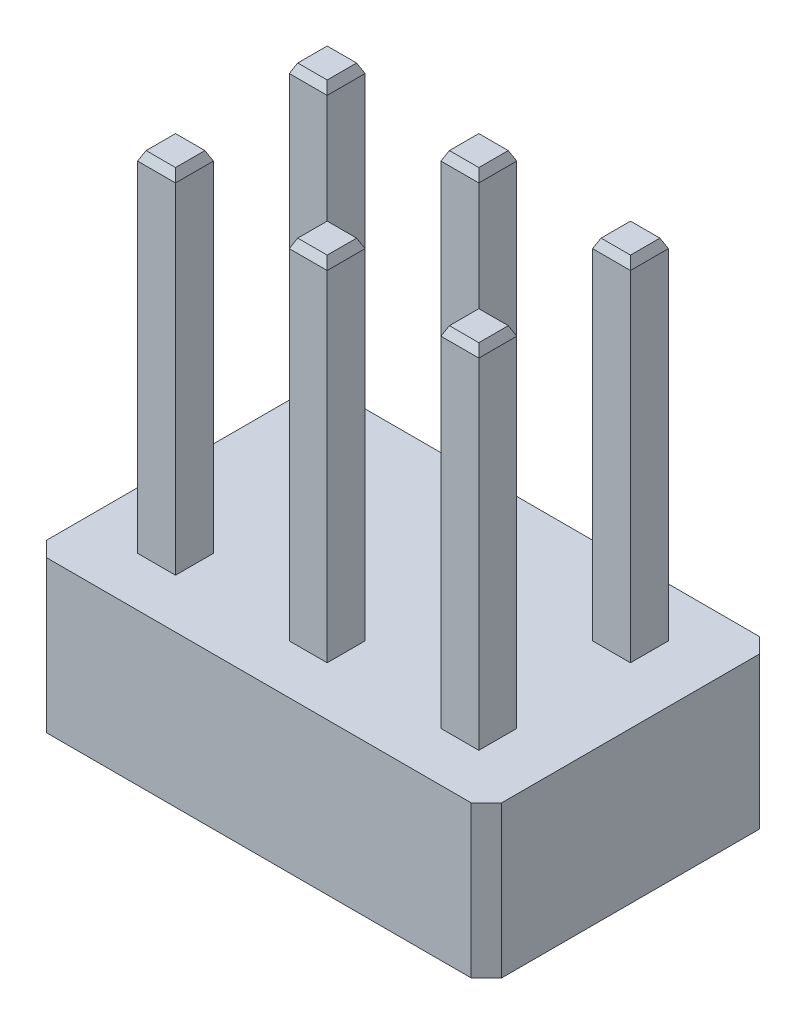
SolidWorks part; units mm, degrees
material "ABS PC"
ref_plane "Front Plane" through (0, 0, 0) normal (0, 0, 1) x (1, 0, 0)
ref_plane "Top Plane" through (0, 0, 0) normal (0, 1, 0) x (1, 0, 0)
ref_plane "Right Plane" through (0, 0, 0) normal (1, 0, 0) x (0, 0, -1)
sketch "Sketch1" plane through (0, 0, 0) normal (0, 1, 0) x (1, 0, 0)
  line L1 (0, 0) -> (7.62, 0)
  line L2 (0, 0) -> (0, 4.826)
  line L3 (0, 4.826) -> (7.62, 4.826)
  line L4 (7.62, 0) -> (7.62, 4.826)
  dimension "D1" = 7.62
  dimension "D2" = 4.826
extrude "Boss-Extrude1" add sketch "Sketch1" along normal blind 2.54
sketch "Sketch2" plane through (0, 2.54, 0) normal (0, 1, 0) x (1, 0, 0)
  line L0 (0, 0) -> (7.62, 0) construction
  line L1 (0.9525, 0.8255) -> (1.5875, 0.8255)
  line L2 (0.9525, 0.8255) -> (0.9525, 1.4605)
  line L3 (0.9525, 1.4605) -> (1.5875, 1.4605)
  line L4 (1.5875, 0.8255) -> (1.5875, 1.4605)
  line L5 (0.9525, 0.8255) -> (1.5875, 1.4605) construction
  line L6 (0.9525, 1.4605) -> (1.5875, 0.8255) construction
  line L7 (0, 4.826) -> (0, 0) construction
  point P0 (1.27, 1.143)
  dimension "D1" = 0.635
  dimension "D2" = 0.635
  dimension "D3" = 1.143
  dimension "D4" = 1.27
extrude "Boss-Extrude2" add sketch "Sketch2" along normal blind 5.842
chamfer "Chamfer2" distance 0.1524 angle 25 4 edges at (1.27, 8.382, -0.8255) (0.9525, 8.382, -1.143) (1.27, 8.382, -1.4605) (1.5875, 8.382, -1.143)
chamfer "Chamfer1" distance 0.254 angle 45 4 edges at (7.62, 1.27, -4.826) (7.62, 1.27, 0) (0, 1.27, -4.826) (0, 1.27, 0)
pattern_linear "LPattern2" count 3 spacing 2.54 along (1, 0, 0) count 2 spacing 2.54 along (0, 0, -1) of "Boss-Extrude2", "Chamfer2"
